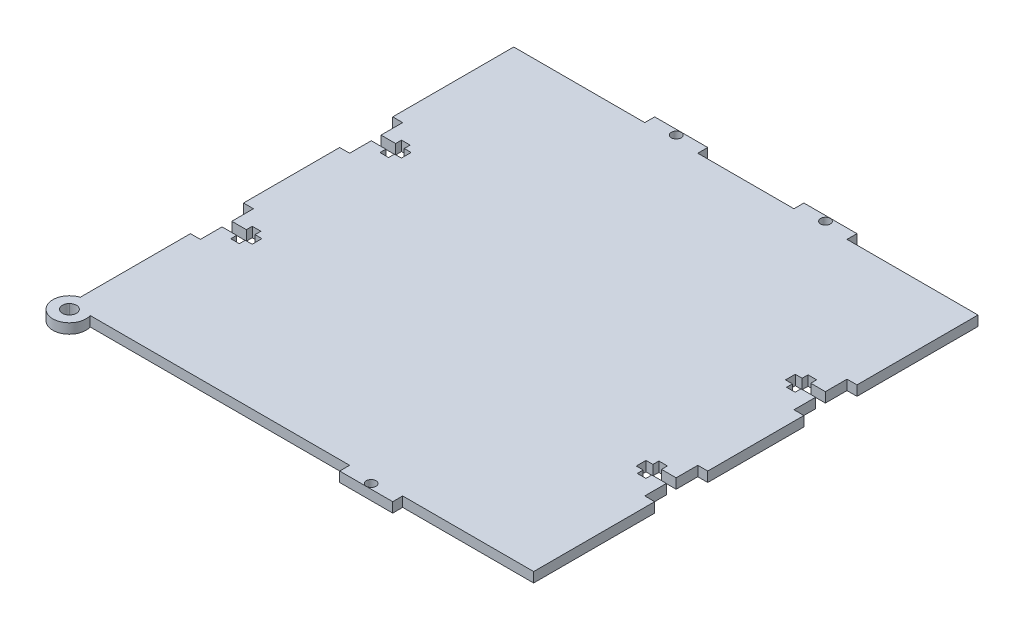
SolidWorks part; units mm, degrees
ref_plane "Front Plane" through (0, 0, 0) normal (0, 0, 1) x (1, 0, 0)
ref_plane "Top Plane" through (0, 0, 0) normal (0, 1, 0) x (1, 0, 0)
ref_plane "Right Plane" through (0, 0, 0) normal (1, 0, 0) x (0, 0, -1)
sketch "Sketch1" plane through (0, 0, 0) normal (0, 1, 0) x (1, 0, 0)
  line L1 (-70, -70) -> (70, -70)
  line L2 (-70, -70) -> (-70, 70)
  line L3 (-70, 70) -> (70, 70)
  line L4 (70, -70) -> (70, 70)
  line L5 (-70, -70) -> (70, 70) construction
  line L6 (-70, 70) -> (70, -70) construction
  point P0 (0, 0)
  dimension "D1" = 140
extrude "Boss-Extrude1" add sketch "Sketch1" along normal blind 3
sketch "Sketch2" plane through (0, 3, 0) normal (0, 1, 0) x (1, 0, 0)
  line L0 (-70, 67) -> (-30.5, 67)
  line L1 (-70, 70) -> (-70, -70) construction
  line L2 (-30.5, 67) -> (-30.5, 70)
  line L3 (70, 70) -> (-70, 70) construction
  line L4 (-30.5, 70) -> (-70, 70)
  line L5 (-70, 70) -> (-70, 67)
  line L6 (-1.65, 0) -> (1.65, 0) construction
  line L7 (-30.5, -70) -> (-70, -70)
  line L8 (-30.5, -67) -> (-30.5, -70)
  line L9 (-70, -67) -> (-30.5, -67)
  line L10 (-70, -70) -> (-70, -67)
  line L11 (0, -1.65) -> (0, 1.65) construction
  line L12 (30.5, -67) -> (30.5, -70)
  line L13 (70, -67) -> (30.5, -67)
  line L14 (70, -70) -> (70, -67)
  line L15 (30.5, -70) -> (70, -70)
  line L16 (30.5, 70) -> (70, 70)
  line L17 (30.5, 67) -> (30.5, 70)
  line L18 (70, 67) -> (30.5, 67)
  line L19 (70, 70) -> (70, 67)
  line L20 (-14.5, 70) -> (-14.5, 67)
  line L21 (-14.5, 67) -> (14.5, 67)
  line L22 (14.5, 67) -> (14.5, 70)
  line L23 (14.5, 70) -> (-14.5, 70)
  line L24 (14.5, -67) -> (14.5, -70)
  line L25 (-14.5, -67) -> (14.5, -67)
  line L26 (-14.5, -70) -> (-14.5, -67)
  line L27 (14.5, -70) -> (-14.5, -70)
  dimension "D1" = 39.5
  dimension "D2" = 3
  dimension "D3" = 3
  dimension "D4" = 29
  dimension "D5" = 55.5
extrude "Cut-Extrude2" cut sketch "Sketch2" against normal blind 3
sketch "Sketch4" plane through (0, 3, 0) normal (0, 1, 0) x (1, 0, 0)
  line L0 (-70, 30.5) -> (-67, 30.5)
  line L1 (-70, 67) -> (-70, -67) construction
  line L2 (-67, 30.5) -> (-67, 14.5)
  line L3 (-67, 14.5) -> (-70, 14.5)
  line L4 (-70, 14.5) -> (-70, 30.5)
  line L5 (-70, 67) -> (-30.5, 67) construction
  line L6 (-1.65, 0) -> (1.65, 0) construction
  line L7 (-67, -14.5) -> (-70, -14.5)
  line L8 (-67, -30.5) -> (-67, -14.5)
  line L9 (-70, -30.5) -> (-67, -30.5)
  line L10 (-70, -14.5) -> (-70, -30.5)
  line L11 (0, -1.65) -> (0, 1.65) construction
  line L12 (67, 14.5) -> (70, 14.5)
  line L13 (67, 30.5) -> (67, 14.5)
  line L14 (70, 30.5) -> (67, 30.5)
  line L15 (70, 14.5) -> (70, 30.5)
  line L16 (67, -30.5) -> (67, -14.5)
  line L17 (70, -30.5) -> (67, -30.5)
  line L18 (70, -14.5) -> (70, -30.5)
  line L19 (67, -14.5) -> (70, -14.5)
  dimension "D1" = 16
  dimension "D2" = 3
  dimension "D3" = 36.5
extrude "Cut-Extrude3" cut sketch "Sketch4" against normal blind 3
sketch "Sketch6" plane through (0, 0, 0) normal (0, -1, 0) x (1, 0, 0)
  line L0 (-30.5, 68.5) -> (-14.5, 68.5) construction
  line L1 (-30.5, 70) -> (-30.5, 67) construction
  line L2 (-14.5, 67) -> (-14.5, 70) construction
  line L3 (30.5, 68.5) -> (14.5, 68.5) construction
  line L4 (30.5, 67) -> (30.5, 70) construction
  line L5 (14.5, 70) -> (14.5, 67) construction
  circle A0 centre (-22.5, 68.5) radius 1.47
  circle A1 centre (22.5, 68.5) radius 1.47
  dimension "D1" = 2.94
extrude "Cut-Extrude4" cut sketch "Sketch6" against normal through all
mirror "Mirror1" about plane through (0, 0, 0) normal (0, 0, 1) of "Cut-Extrude4"
sketch "Sketch7" plane through (0, 0, 0) normal (0, -1, 0) x (-1, 0, 0)
  line L0 (67, -22.5) -> (-67, -22.5) construction
  line L1 (67, -30.5) -> (67, -14.5) construction
  line L2 (-67, -14.5) -> (-67, -30.5) construction
  line L3 (67, -23.97) -> (62.6, -23.97)
  line L4 (62.6, -23.97) -> (62.6, -25.75)
  line L5 (62.6, -25.75) -> (60, -25.75)
  line L6 (60, -25.75) -> (60, -23.97)
  line L7 (60, -23.97) -> (57.92, -23.97)
  line L8 (57.92, -23.97) -> (57.92, -21.03)
  line L9 (67, -23.97) -> (67, -21.03)
  line L10 (67, -21.03) -> (62.6, -21.03)
  line L11 (62.6, -21.03) -> (62.6, -19.25)
  line L12 (62.6, -19.25) -> (60, -19.25)
  line L13 (60, -19.25) -> (60, -21.03)
  line L14 (60, -21.03) -> (57.92, -21.03)
  line L16 (0, 1.65) -> (0, -1.65) construction
  line L17 (-67, -23.97) -> (-67, -21.03)
  line L18 (-67, -23.97) -> (-62.6, -23.97)
  line L19 (-62.6, -23.97) -> (-62.6, -25.75)
  line L20 (-62.6, -25.75) -> (-60, -25.75)
  line L21 (-60, -25.75) -> (-60, -23.97)
  line L22 (-60, -23.97) -> (-57.92, -23.97)
  line L23 (-57.92, -23.97) -> (-57.92, -21.03)
  line L24 (-60, -21.03) -> (-57.92, -21.03)
  line L25 (-60, -19.25) -> (-60, -21.03)
  line L26 (-62.6, -19.25) -> (-60, -19.25)
  line L27 (-62.6, -21.03) -> (-62.6, -19.25)
  line L28 (-67, -21.03) -> (-62.6, -21.03)
  line L29 (-1.65, 0) -> (1.65, 0) construction
  line L30 (-67, 23.97) -> (-62.6, 23.97)
  line L31 (-62.6, 23.97) -> (-62.6, 25.75)
  line L32 (-62.6, 25.75) -> (-60, 25.75)
  line L33 (-60, 25.75) -> (-60, 23.97)
  line L34 (-60, 23.97) -> (-57.92, 23.97)
  line L35 (-57.92, 23.97) -> (-57.92, 21.03)
  line L36 (-60, 21.03) -> (-57.92, 21.03)
  line L37 (-60, 19.25) -> (-60, 21.03)
  line L38 (-62.6, 19.25) -> (-60, 19.25)
  line L39 (-62.6, 21.03) -> (-62.6, 19.25)
  line L40 (-67, 21.03) -> (-62.6, 21.03)
  line L41 (-67, 23.97) -> (-67, 21.03)
  line L42 (67, 23.97) -> (67, 21.03)
  line L43 (67, 23.97) -> (62.6, 23.97)
  line L44 (62.6, 23.97) -> (62.6, 25.75)
  line L45 (62.6, 25.75) -> (60, 25.75)
  line L46 (60, 25.75) -> (60, 23.97)
  line L47 (60, 23.97) -> (57.92, 23.97)
  line L48 (57.92, 23.97) -> (57.92, 21.03)
  line L49 (60, 21.03) -> (57.92, 21.03)
  line L50 (60, 19.25) -> (60, 21.03)
  line L51 (62.6, 19.25) -> (60, 19.25)
  line L52 (62.6, 21.03) -> (62.6, 19.25)
  line L53 (67, 21.03) -> (62.6, 21.03)
  point P19 (57.92, -22.5)
  dimension "D1" = 1.78
  dimension "D2" = 2.6
  dimension "D3" = 2.08
  dimension "D4" = 4.4
  dimension "D5" = 2.94
extrude "Cut-Extrude5" cut sketch "Sketch7" against normal blind 3
sketch "Sketch8" plane through (0, 0, 0) normal (0, -1, 0) x (-1, 0, 0)
  line L0 (30.5, -67) -> (14.5, -67)
  line L1 (30.5, -67) -> (30.5, -70)
  line L2 (30.5, -70) -> (14.5, -70)
  line L3 (14.5, -70) -> (14.5, -67)
extrude "Cut-Extrude6" cut sketch "Sketch8" against normal blind 3
sketch "Sketch9" plane through (0, 0, 0) normal (0, -1, 0) x (-1, 0, 0)
  line L0 (70, -67) -> (70, -68.5)
  line L1 (70, -68.5) -> (67, -68.5)
  line L2 (67, -68.5) -> (67, -67)
  line L3 (-14.5, -67) -> (70, -67) construction
  line L4 (67, -67) -> (70, -67)
  circle A0 centre (68.5, -68.5) radius 2.12
  circle A1 centre (68.5, -68.5) radius 5
  dimension "D2" = 4.24
  dimension "D3" = 10
  dimension "D1" = 3
  dimension "D4" = 1.5
extrude "Boss-Extrude3" add sketch "Sketch9" against normal blind 3 contours A1 A0
sketch "Sketch10" plane through (0, 3, 0) normal (0, 1, 0) x (1, 0, 0)
  circle A0 centre (-68.5, -68.5) radius 2.12
  dimension "D1" = 4.24
extrude "Cut-Extrude7" cut sketch "Sketch10" against normal blind 3
